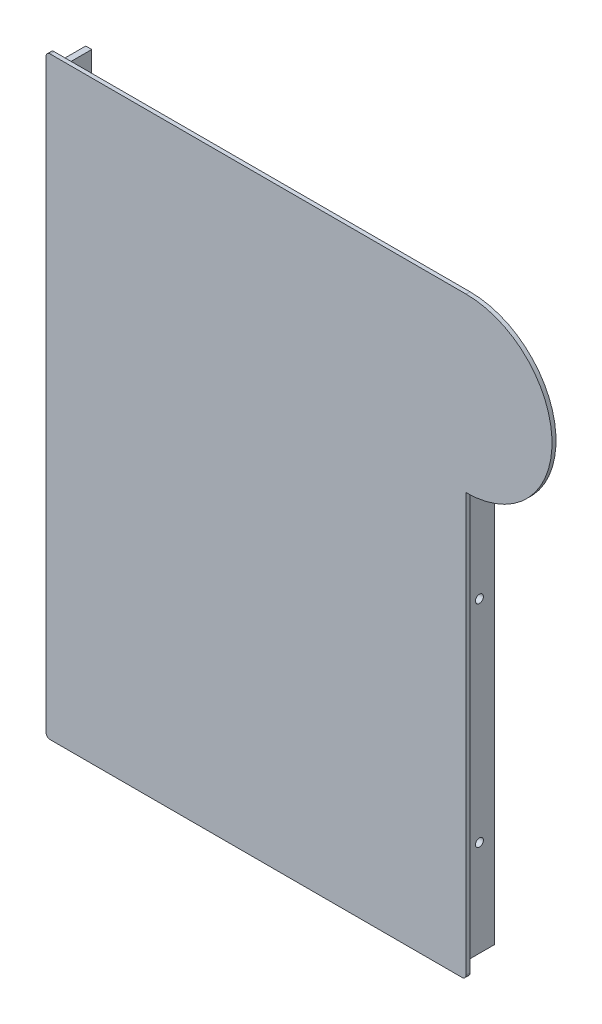
SolidWorks part; units mm, degrees
ref_plane "前视基准面" through (0, 0, 0) normal (0, 0, 1) x (1, 0, 0)
ref_plane "上视基准面" through (0, 0, 0) normal (0, 1, 0) x (1, 0, 0)
ref_plane "右视基准面" through (0, 0, 0) normal (1, 0, 0) x (0, 0, -1)
sketch "草图1" plane through (0, 0, 0) normal (0, 0, 1) x (1, 0, 0)
  line L8 (0, 53.35) -> (-208, 53.35)
  line L9 (-210, 51.35) -> (-210, -241.65)
  line L10 (-208, -243.65) -> (-2, -243.65)
  line L11 (0, -241.65) -> (0, -32.65)
  arc A8 (-208, 53.35) -> (-210, 51.35) centre (-208, 51.35) ccw
  arc A9 (-210, -241.65) -> (-208, -243.65) centre (-208, -241.65) ccw
  arc A10 (-2, -243.65) -> (0, -241.65) centre (-2, -241.65) ccw
  arc A11 (0, -32.65) -> (0, 53.35) centre (0, 10.35) ccw
extrude "凸台-拉伸1" add sketch "草图1" along normal blind 2
sketch "草图3" plane through (0, 0, 0) normal (0, 0, -1) x (-1, 0, 0)
  line L0 (207.2, 48.6877) -> (207.2, -238.4546)
  line L1 (207.2, -238.4546) -> (205.1304, -240.85)
  line L2 (205.1304, -240.85) -> (5.6826, -240.85)
  line L3 (5.6826, -240.85) -> (2.8, -238.3595)
  line L4 (2.8, -238.3595) -> (2.8, -37.1279)
  line L5 (205.5, -241.15) -> (4.5, -241.15) construction
  line L6 (207.5, 48.85) -> (207.5, -239.15) construction
  line L7 (2.5, -239.15) -> (2.5, -32.5773) construction
  dimension "D1" = 0.3
  dimension "D2" = 0.3
  dimension "D3" = 0.3
extrude "拉伸-薄壁1" add sketch "草图3" along normal blind 15 thin
sketch "草图4" plane through (0, -240.85, 0) normal (0, -1, 0) x (1, 0, 0)
  line L0 (-105, 2) -> (-105, -14.176) construction
  line L1 (-208, 2) -> (-2, 2) construction
  circle A0 centre (-167.8079, -7.5) radius 2
  circle A1 centre (-42.1921, -7.5) radius 2
extrude "切除-拉伸1" cut sketch "草图4" against normal blind 15
sketch "草图5" plane through (-207.2, 0, 0) normal (-1, 0, 0) x (0, 0, 1)
  line L0 (-15, -137.5758) -> (2, -137.5758) construction
  line L1 (-15, 48.6877) -> (-15, -238.4546) construction
  line L2 (2, 51.35) -> (2, -241.65) construction
  circle A0 centre (-7.5, -190.3505) radius 2
  circle A1 centre (-7.5, -84.8011) radius 2
extrude "切除-拉伸2" cut sketch "草图5" against normal blind 283
sketch "草图6" plane through (0, 0, 0) normal (0, 0, -1) x (-1, 0, 0)
  line L1 (-67.999, 61.4883) -> (243.7926, 61.4883)
  line L2 (-67.999, 61.4883) -> (-67.999, -109.8192)
  line L3 (-67.999, -109.8192) -> (243.7926, -109.8192)
  line L4 (243.7926, 61.4883) -> (243.7926, -109.8192)
extrude "切除-拉伸3" [suppressed] cut sketch "草图6" against normal mid plane 111 flip side to cut
